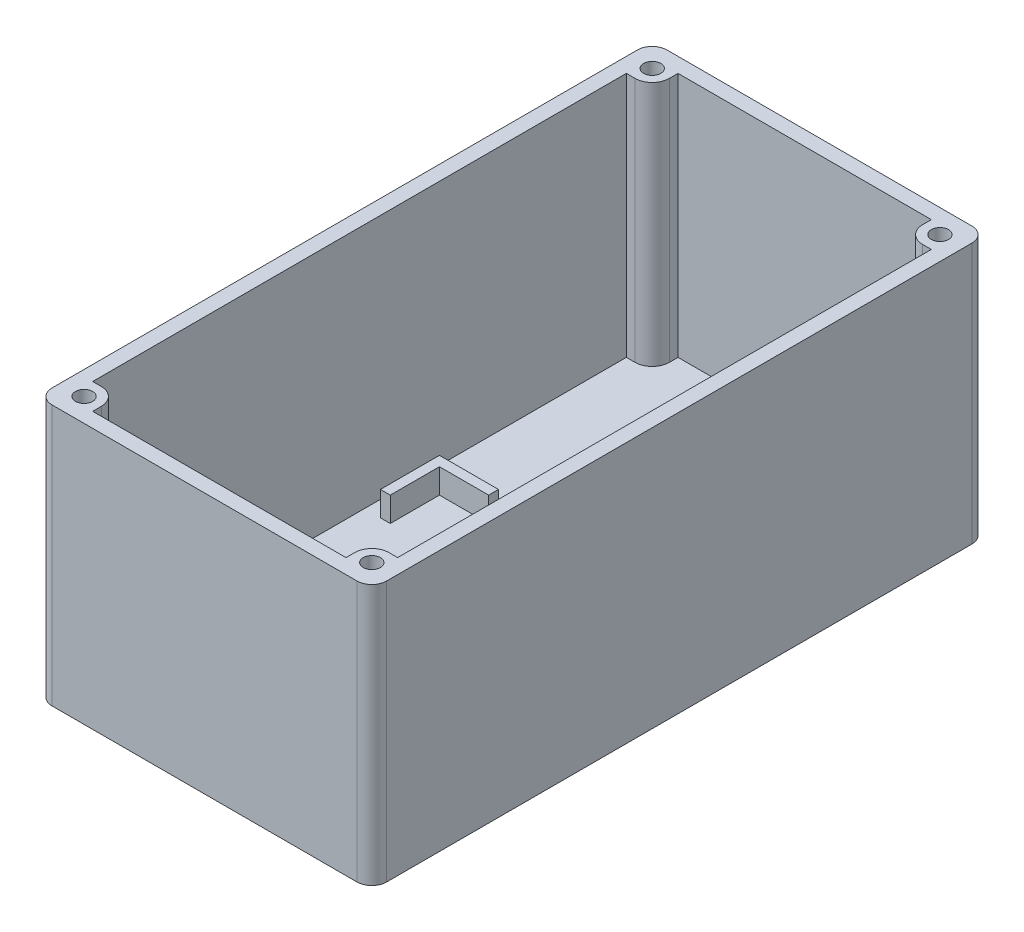
SolidWorks part; units mm, degrees
ref_plane "Спереди" through (0, 0, 0) normal (0, 0, 1) x (1, 0, 0)
ref_plane "Сверху" through (0, 0, 0) normal (0, 1, 0) x (1, 0, 0)
ref_plane "Справа" through (0, 0, 0) normal (1, 0, 0) x (0, 0, -1)
sketch "Эскиз1" plane through (0, 0, 0) normal (0, 1, 0) x (1, 0, 0)
  line L1 (34, 62.5) -> (-34, 62.5)
  line L2 (34, 62.5) -> (34, -62.5)
  line L3 (34, -62.5) -> (-34, -62.5)
  line L4 (-34, 62.5) -> (-34, -62.5)
  line L5 (34, 62.5) -> (-34, -62.5) construction
  line L6 (34, -62.5) -> (-34, 62.5) construction
  point P0 (0, 0)
  dimension "D1" = 68
  dimension "D2" = 125
extrude "Бобышка-Вытянуть1" add sketch "Эскиз1" along normal blind 3
sketch "Эскиз3" plane through (0, 3, 0) normal (0, 1, 0) x (1, 0, 0)
  line L1 (34, -62.5) -> (-34, -62.5)
  line L2 (34, -62.5) -> (34, 62.5)
  line L3 (34, 62.5) -> (-34, 62.5)
  line L4 (-34, -62.5) -> (-34, 62.5)
  line L5 (34, -62.5) -> (-34, 62.5) construction
  line L6 (34, 62.5) -> (-34, -62.5) construction
  point P0 (0, 0)
extrude "Вытянуть-Тонкостенный1" add sketch "Эскиз3" along normal blind 50 thin
fillet "Скругление1" radius 3 4 edges at (34, 26.5, -62.5) (-34, 26.5, -62.5) (-34, 26.5, 62.5) (34, 26.5, 62.5)
sketch "Эскиз4" plane through (0, 3, 0) normal (0, 1, 0) x (1, 0, 0)
  line L0 (-31, -62.5) -> (31, -62.5) construction
  line L3 (-25.75, -59.5) -> (25.75, -59.5)
  line L5 (-31, -59.5) -> (31, -59.5) construction
  line L6 (-25.75, 11) -> (-25.75, 1)
  line L7 (-25.75, 1) -> (-27.75, 1)
  line L8 (-27.75, 1) -> (-27.75, 13)
  line L9 (-27.75, 13) -> (-15.75, 13)
  line L10 (-15.75, 13) -> (-15.75, 11)
  line L11 (-15.75, 11) -> (-25.75, 11)
  line L12 (0, 59.5) -> (0, -59.5) construction
  line L13 (31, 59.5) -> (-31, 59.5) construction
  line L14 (15.75, 11) -> (25.75, 11)
  line L15 (15.75, 13) -> (15.75, 11)
  line L16 (27.75, 13) -> (15.75, 13)
  line L17 (27.75, 1) -> (27.75, 13)
  line L18 (25.75, 1) -> (27.75, 1)
  line L19 (25.75, 11) -> (25.75, 1)
  line L21 (-25.75, -59.5) -> (-27.75, -59.5)
  line L22 (-25.75, -59.5) -> (-25.75, -49.5)
  line L23 (-25.75, -49.5) -> (-27.75, -49.5)
  line L24 (-27.75, -59.5) -> (-27.75, -49.5)
  line L25 (25.75, -59.5) -> (27.75, -59.5)
  line L26 (25.75, -59.5) -> (25.75, -49.5)
  line L27 (25.75, -49.5) -> (27.75, -49.5)
  line L28 (27.75, -59.5) -> (27.75, -49.5)
  point P6 (0, -62.5)
  point P7 (0, -59.5)
  point P10 (0, -59.5)
  line M9 (-31, -59.5) -> (31, -59.5)
  dimension "D1" = 51.5
  dimension "D2" = 70.5
  dimension "D3" = 10
  dimension "D4" = 10
  dimension "D5" = 2
  dimension "D6" = 2
  dimension "D7" = 10
  dimension "D8" = 10
extrude "Бобышка-Вытянуть2" add sketch "Эскиз4" along normal blind 5 contours L14 L19 L18 L17 L16 L15 | L28 L27 L26 M9 | L24 L22 L23 M9 | L9 L10 L11 L6 L7 L8
sketch "Эскиз5" plane through (0, 53, 0) normal (0, 1, 0) x (1, 0, 0)
  line L0 (0, 62.5) -> (0, -62.5) construction
  line L1 (31, 62.5) -> (-31, 62.5) construction
  line L2 (-31, -62.5) -> (31, -62.5) construction
  line L3 (-34, 0) -> (34, 0) construction
  line L4 (-34, 59.5) -> (-34, -59.5) construction
  line L5 (34, -59.5) -> (34, 59.5) construction
  line L6 (31, 59.5) -> (-31, 59.5) construction
  line L8 (-31, 59.5) -> (-31, -59.5) construction
  line L9 (-29.25, 54.25) -> (-32.75, 54.25)
  line L10 (-32.75, 54.25) -> (-32.75, 57.75)
  line L11 (-25.75, 57.75) -> (-25.75, 61.25)
  line L12 (-25.75, 61.25) -> (-29.25, 61.25)
  line L13 (25.75, 61.25) -> (29.25, 61.25)
  line L14 (25.75, 57.75) -> (25.75, 61.25)
  line L15 (32.75, 54.25) -> (32.75, 57.75)
  line L16 (29.25, 54.25) -> (32.75, 54.25)
  line L17 (29.25, -54.25) -> (32.75, -54.25)
  line L18 (32.75, -54.25) -> (32.75, -57.75)
  line L19 (25.75, -57.75) -> (25.75, -61.25)
  line L20 (25.75, -61.25) -> (29.25, -61.25)
  line L21 (-25.75, -61.25) -> (-29.25, -61.25)
  line L22 (-25.75, -57.75) -> (-25.75, -61.25)
  line L23 (-32.75, -54.25) -> (-32.75, -57.75)
  line L24 (-29.25, -54.25) -> (-32.75, -54.25)
  circle A0 centre (-29.25, 57.75) radius 1.75
  arc A1 (-29.25, 54.25) -> (-25.75, 57.75) centre (-29.25, 57.75) ccw
  arc A2 (-29.25, 61.25) -> (-32.75, 57.75) centre (-29.25, 57.75) ccw
  arc A3 (29.25, 61.25) -> (32.75, 57.75) centre (29.25, 57.75) cw
  arc A4 (29.25, 54.25) -> (25.75, 57.75) centre (29.25, 57.75) cw
  circle A5 centre (29.25, 57.75) radius 1.75
  circle A6 centre (29.25, -57.75) radius 1.75
  arc A7 (29.25, -54.25) -> (25.75, -57.75) centre (29.25, -57.75) ccw
  arc A8 (29.25, -61.25) -> (32.75, -57.75) centre (29.25, -57.75) ccw
  arc A9 (-29.25, -61.25) -> (-32.75, -57.75) centre (-29.25, -57.75) cw
  arc A10 (-29.25, -54.25) -> (-25.75, -57.75) centre (-29.25, -57.75) cw
  circle A11 centre (-29.25, -57.75) radius 1.75
  dimension "D1" = 3.5
  dimension "D2" = 7
extrude "Бобышка-Вытянуть3" add sketch "Эскиз5" against normal up to surface (50 mm away) up to face at (-23.0833, 3, -8.3333)
sketch "Эскиз6" plane through (0, 53, 0) normal (0, 1, 0) x (1, 0, 0)
  line L0 (0, 62.5) -> (0, -62.5) construction
  line L1 (31, 62.5) -> (-31, 62.5) construction
  line L2 (-31, -62.5) -> (31, -62.5) construction
  line L3 (-34, 0) -> (34, 0) construction
  line L4 (-34, 59.5) -> (-34, -59.5) construction
  line L5 (34, -59.5) -> (34, 59.5) construction
  circle A0 centre (-29.25, 57.75) radius 1.75
  circle A1 centre (29.25, 57.75) radius 1.75
  circle A2 centre (29.25, -57.75) radius 1.75
  circle A3 centre (-29.25, -57.75) radius 1.75
extrude "Вырез-Вытянуть1" cut sketch "Эскиз6" against normal through all
